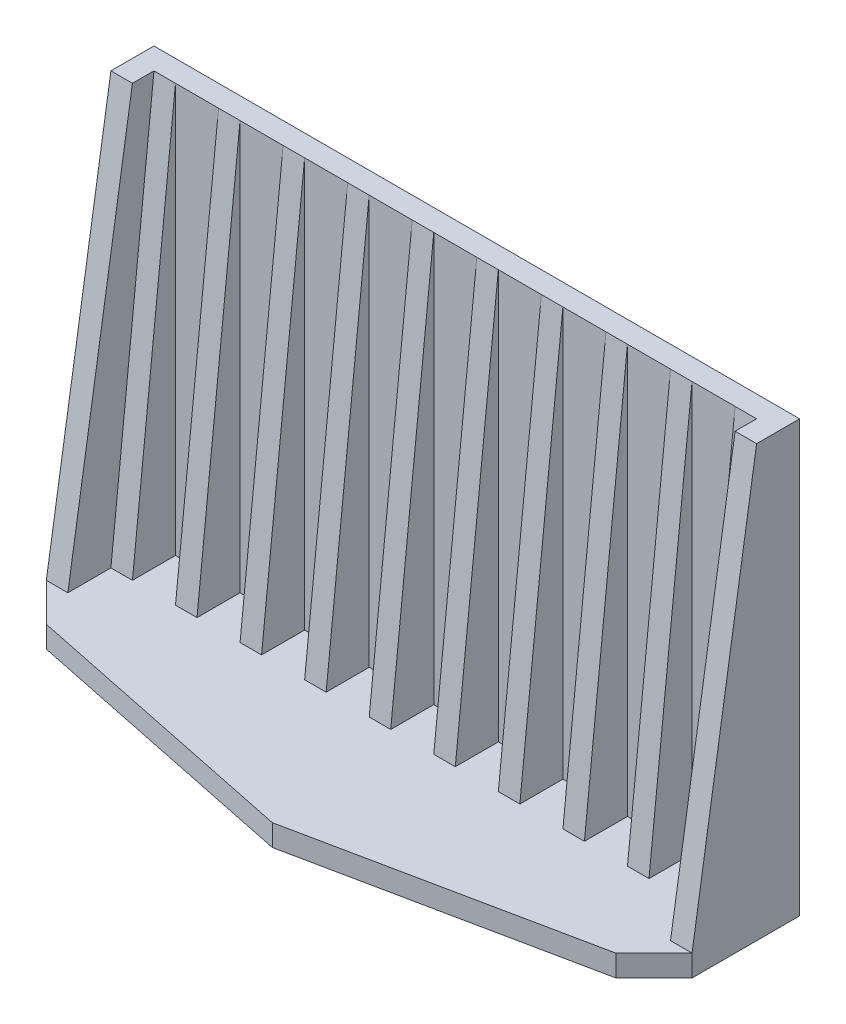
SolidWorks part; units mm, degrees
ref_plane "Alzado" through (0, 0, 0) normal (0, 0, 1) x (1, 0, 0)
ref_plane "Planta" through (0, 0, 0) normal (0, 1, 0) x (1, 0, 0)
ref_plane "Vista lateral" through (0, 0, 0) normal (1, 0, 0) x (0, 0, -1)
sketch "Croquis1" plane through (0, 0, 0) normal (1, 0, 0) x (0, 0, -1)
  line L0 (0, 0) -> (1, 0)
  line L1 (1, 0) -> (1, 20)
  line L2 (0, 0) -> (0, 20)
  line L3 (0, 20) -> (1, 20)
  dimension "D1" = 1
  dimension "D2" = 20
extrude "Saliente-Extruir1" add sketch "Croquis1" against normal blind 30
sketch "Croquis2" plane through (0, 0, 0) normal (1, 0, 0) x (0, 0, -1)
  line L0 (0, 0) -> (-4, 0)
  line L1 (-4, 0) -> (-4, 1)
  line L5 (-4, 1) -> (0, 1)
  line L6 (0, 20) -> (0, 0) construction
  line L7 (0, 1) -> (0, 0)
extrude "Saliente-Extruir3" add sketch "Croquis2" against normal blind 30
sketch "Croquis3" plane through (0, 0, 0) normal (1, 0, 0) x (0, 0, -1)
  line L0 (-4, 1) -> (-1, 20)
  line L1 (-1, 20) -> (0, 20)
  line L2 (0, 1) -> (-4, 1)
  line L3 (0, 1) -> (0, 20)
extrude "Saliente-Extruir4" add sketch "Croquis3" against normal blind 1 contours L3 L1 L0 L2
sketch "Croquis6" plane through (-30, 0, 0) normal (-1, 0, 0) x (0, 0, 1)
  line L0 (0, 20) -> (1, 20)
  line L1 (1, 20) -> (4, 1)
  line L2 (4, 1) -> (0, 1)
  line L3 (0, 1) -> (0, 20)
extrude "Saliente-Extruir5" add sketch "Croquis6" against normal blind 1
sketch "Croquis7" plane through (0, 1, 0) normal (0, 1, 0) x (1, 0, 0)
  line L0 (-30, -4) -> (-28.2322, -5.7678)
  line L1 (0, -4) -> (-1.7678, -5.7678)
  line L2 (-28.2322, -5.7678) -> (-15, -8.5)
  line L3 (-30, -4) -> (0, -4)
  line L5 (-1.7678, -5.7678) -> (-15, -8.5)
extrude "Saliente-Extruir7" add sketch "Croquis7" against normal blind 1
sketch "Croquis8" plane through (-29, 0, 0) normal (1, 0, 0) x (0, 0, -1)
  line L1 (0, 1) -> (-4, 1) construction
  line L2 (-2, 1) -> (0, 20)
rib "Nervio4" sketch "Croquis8" sketch "Croquis8" thickness 1 parameters "D1"=1
pattern_linear "MatrizL12" count 9 spacing 3 along (1, 0, 0) of "Nervio4"
sketch "Croquis10" plane through (-1, 0, 0) normal (-1, 0, 0) x (0, 0, 1)
  line L1 (0, 1) -> (4, 1) construction
  line L2 (2, 1) -> (0, 20)
rib "Nervio5" sketch "Croquis10" sketch "Croquis10" thickness 1 parameters "D1"=1
